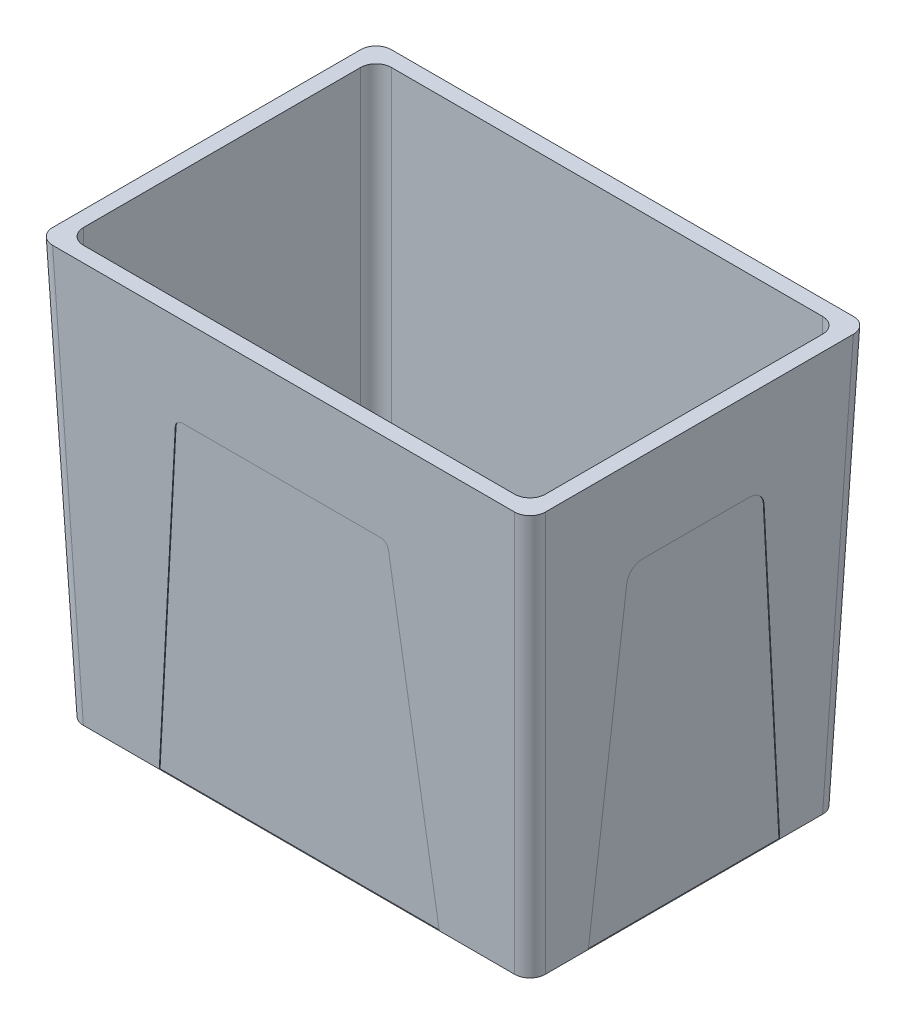
SolidWorks part; units mm, degrees
material "PVC 0.007 Plasticized"
ref_plane "Front Plane" through (0, 0, 0) normal (0, 0, 1) x (1, 0, 0)
ref_plane "Top Plane" through (0, 0, 0) normal (0, 1, 0) x (1, 0, 0)
ref_plane "Right Plane" through (0, 0, 0) normal (1, 0, 0) x (0, 0, -1)
sketch "Sketch1" plane through (0, 0, 0) normal (0, 1, 0) x (1, 0, 0)
  line L1 (-150, 100) -> (150, 100)
  line L2 (-150, 100) -> (-150, -100)
  line L3 (-150, -100) -> (150, -100)
  line L4 (150, 100) -> (150, -100)
  line L5 (-150, 100) -> (150, -100) construction
  line L6 (-150, -100) -> (150, 100) construction
  point P0 (0, 0)
  dimension "D1" = 300
  dimension "D2" = 200
ref_plane "Plane1" through (0, 270, 0) normal (0, 1, 0) x (1, 0, 0)
sketch "Sketch2" plane through (0, 270, 0) normal (0, 1, 0) x (1, 0, 0)
  line L1 (-160, 110) -> (160, 110)
  line L2 (-160, 110) -> (-160, -110)
  line L3 (-160, -110) -> (160, -110)
  line L4 (160, 110) -> (160, -110)
  line L5 (-160, 110) -> (160, -110) construction
  line L6 (-160, -110) -> (160, 110) construction
  point P0 (0, 0)
  dimension "D1" = 320
  dimension "D2" = 220
loft "Loft1" add profiles "Sketch1", "Sketch2"
fillet "Fillet1" radius 10 4 edges
sketch "Sketch3" plane through (0, 270, 0) normal (0, 1, 0) x (1, 0, 0)
  line L1 (-140, 100) -> (140, 100)
  line L2 (-150, 90) -> (-150, -90)
  line L3 (-140, -100) -> (140, -100)
  line L4 (150, 90) -> (150, -90)
  line L5 (-150, 100) -> (150, -100) construction
  line L6 (-150, -100) -> (150, 100) construction
  arc A0 (-150, -90) -> (-140, -100) centre (-140, -90) ccw
  arc A1 (140, -100) -> (150, -90) centre (140, -90) ccw
  arc A2 (140, 100) -> (150, 90) centre (140, 90) cw
  arc A3 (-140, 100) -> (-150, 90) centre (-140, 90) ccw
  point P0 (0, 0)
  dimension "D3" = 10
  dimension "D1" = 300
  dimension "D2" = 200
extrude "Cut-Extrude1" cut sketch "Sketch3" against normal blind 250
sketch "Sketch4" plane through (0, -3.6986, 99.863) normal (0, -0.037, 0.9993) x (1, 0, 0)
  line L0 (-90.7259, 3.7012) -> (-72.7526, 209.1369)
  line L1 (-140.0069, 3.7012) -> (140.0069, 3.7012) construction
  line L2 (90.6683, 6.9353) -> (65.6656, 209.3142)
  line L3 (-67.7717, 213.7012) -> (60.7034, 213.7012)
  line L4 (90.6683, 6.9353) -> (91.0678, 3.7012)
  line L5 (91.0678, 3.7012) -> (-90.7259, 3.7012)
  arc A0 (-72.7526, 209.1369) -> (-67.7717, 213.7012) centre (-67.7717, 208.7012) cw
  arc A1 (60.7034, 213.7012) -> (65.6656, 209.3142) centre (60.7034, 208.7012) cw
  point P9 (-72.3533, 213.7012)
  dimension "D3" = 5
  dimension "D1" = 210
  dimension "D2" = 85
extrude "Cut-Extrude3" cut sketch "Sketch4" against normal blind 0.5
mirror "Mirror1" about plane through (0, 0, 0) normal (0, 0, 1) of "Cut-Extrude3"
sketch "Sketch5" plane through (149.7945, -5.5479, 0) normal (0.9993, -0.037, 0) x (0, 0, -1)
  line L0 (-62.1572, 5.5517) -> (-44.5832, 206.4233)
  line L1 (-90.0069, 5.5517) -> (90.0069, 5.5517) construction
  line L2 (-62.1572, 5.5517) -> (62.1572, 5.5517)
  line L3 (62.1572, 5.5517) -> (44.5832, 206.4233)
  line L4 (-34.6212, 215.5517) -> (34.6212, 215.5517)
  arc A0 (44.5832, 206.4233) -> (34.6212, 215.5517) centre (34.6212, 205.5517) ccw
  arc A1 (-44.5832, 206.4233) -> (-34.6212, 215.5517) centre (-34.6212, 205.5517) cw
  point P11 (-43.7845, 215.5517)
  dimension "D3" = 10
  dimension "D1" = 210
  dimension "D2" = 85
extrude "Cut-Extrude4" cut sketch "Sketch5" against normal blind 0.5
mirror "Mirror2" about plane through (0, 0, 0) normal (1, 0, 0) of "Cut-Extrude4"
